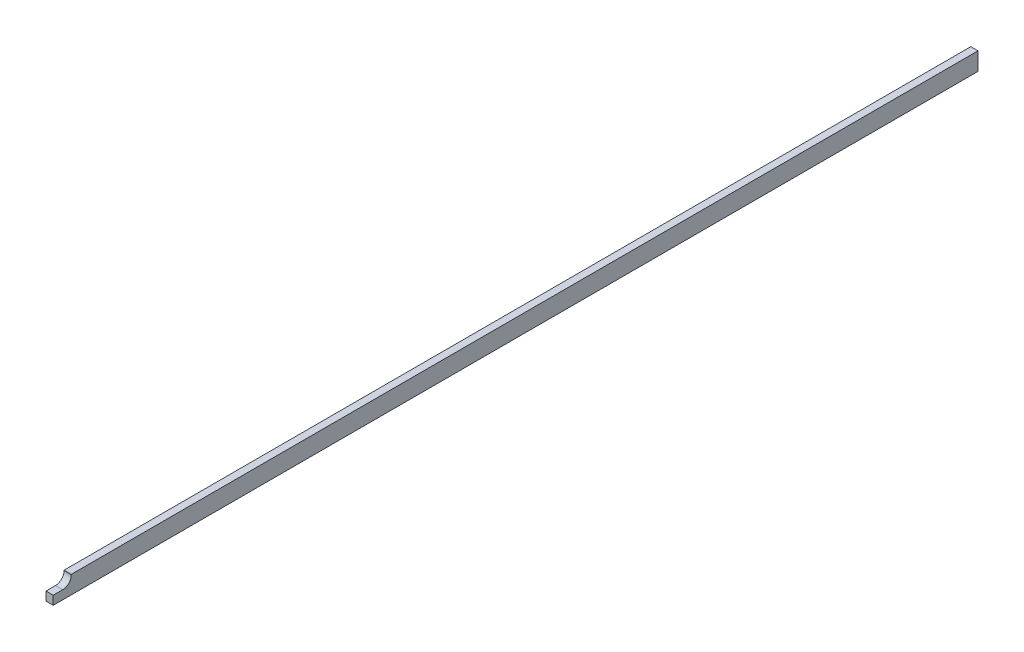
SolidWorks part; units mm, degrees
material "1.4000 (X6Cr13)"
ref_plane "Front Plane" through (0, 0, 0) normal (0, 0, 1) x (1, 0, 0)
ref_plane "Top Plane" through (0, 0, 0) normal (0, 1, 0) x (1, 0, 0)
ref_plane "Right Plane" through (0, 0, 0) normal (1, 0, 0) x (0, 0, -1)
sketch "Sketch1" plane through (0, 0, 0) normal (0, 0, 1) x (1, 0, 0)
  line L1 (-0.8, -1.975) -> (0.8, -1.975)
  line L2 (-0.8, -1.975) -> (-0.8, 1.975)
  line L3 (-0.8, 1.975) -> (0.8, 1.975)
  line L4 (0.8, -1.975) -> (0.8, 1.975)
  line L5 (-0.8, -1.975) -> (0.8, 1.975) construction
  line L6 (-0.8, 1.975) -> (0.8, -1.975) construction
  point P0 (0, 0)
  dimension "D1" = 3.95
  dimension "D2" = 1.6
extrude "Boss-Extrude1" add sketch "Sketch1" along normal blind 205
sketch "Sketch2" plane through (0.8, 0, 0) normal (1, 0, 0) x (0, 0, -1)
  line L1 (-205, 1.975) -> (-201, 1.975)
  line L2 (-205, 1.975) -> (-205, -0.025)
  line L3 (-205, -0.025) -> (-202.9, -0.025)
  line L4 (-201, 1.975) -> (-201, 1.875)
  arc A0 (-202.9, -0.025) -> (-201, 1.875) centre (-202.9, 1.875) ccw
  point P7 (-201, -0.025)
  dimension "D3" = 1.9
  dimension "D1" = 4
  dimension "D2" = 2
extrude "Cut-Extrude1" cut sketch "Sketch2" against normal blind 205
